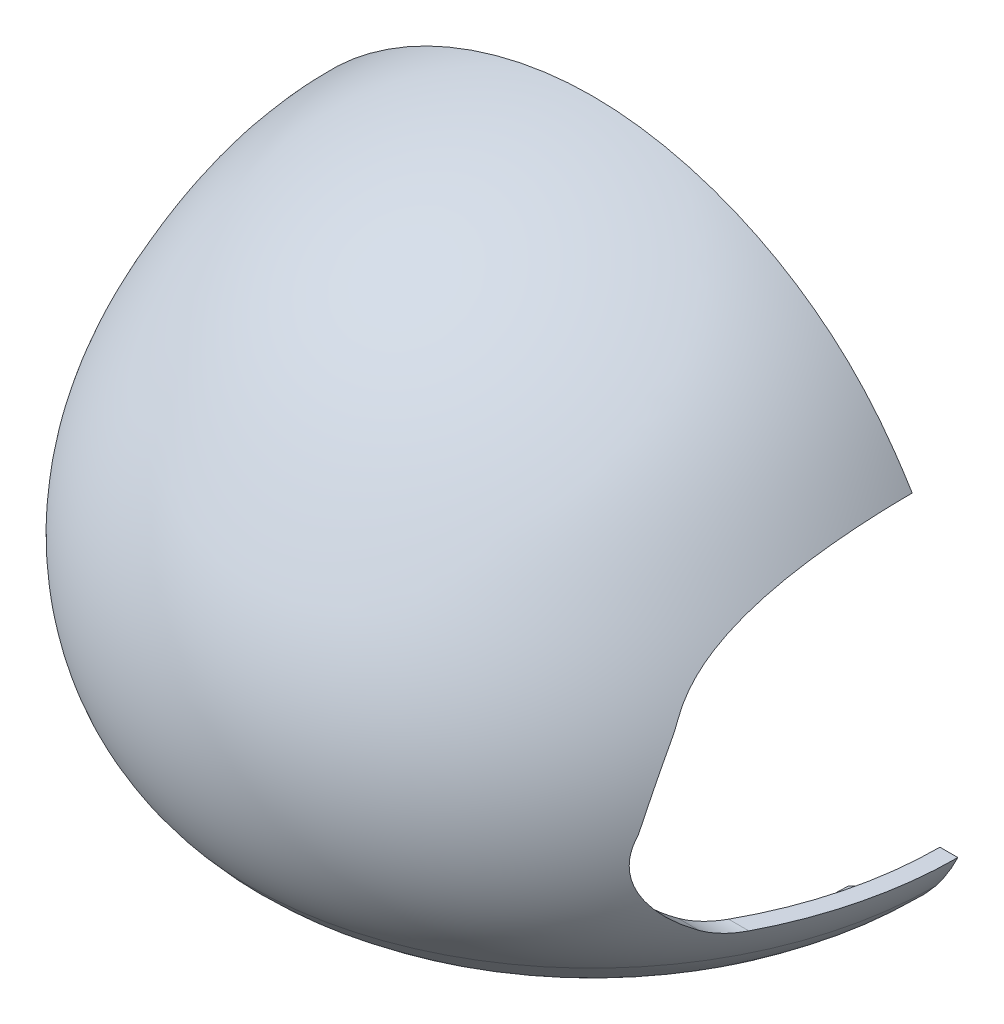
SolidWorks part; units mm, degrees
ref_plane "Front Plane" through (0, 0, 0) normal (0, 0, 1) x (1, 0, 0)
ref_plane "Top Plane" through (0, 0, 0) normal (0, 1, 0) x (1, 0, 0)
ref_plane "Right Plane" through (0, 0, 0) normal (1, 0, 0) x (0, 0, -1)
sketch "Sketch3" plane through (0, 0, 0) normal (0, 0, 1) x (1, 0, 0)
  line L0 (0.0245, 157.0849) -> (0.0245, 152.0849)
  line L1 (0.0245, -20.9434) -> (0.0245, -25.9434)
  line L2 (0.0245, 171.6103) -> (0.0245, -40.6784) construction
  spline S0 degree 3 poles (-103.1746, 0) (-78.8328, -30.0641) (-33.4587, -20.9434) (0.0245, -20.9434) knots 0 0 0 0 1 1 1 1
  spline S1 degree 3 poles (-103.1746, 0) (-114.7602, 14.5762) (-119.8367, 49.2728) (-101.4518, 88.6739) (-71.3798, 134.4794) (-29.75, 152.0849) (0.0245, 152.0849) knots 0 0 0 0 0.250738 0.442513 0.587645 1 1 1 1
  spline S2 degree 1 poles (-107.0747, -3.1288) (0.0245, -25.9434) knots 0 0 1 1 construction
  spline S3 degree 1 poles (-107.0747, -3.1288) (0.0245, 157.0849) knots 0 0 1 1 construction
  spline S4 degree 3 poles (0.0245, -25.9434) (-1.0078, -25.9434) (-3.0527, -25.9607) (-7.3007, -26.054) (-12.7748, -26.2598) (-19.5869, -26.581) (-28.9113, -27.0143) (-40.9004, -27.387) (-55.4438, -26.9753) (-69.7899, -25.0863) (-81.2787, -21.7225) (-89.9598, -17.6028) (-96.1383, -13.7178) (-100.9459, -9.7522) (-104.5344, -6.1303) (-106.2545, -4.1419) (-107.0747, -3.1288) knots -0.000194 -0.000194 -0.000194 -0.000194 0.031062 0.062318 0.12483 0.187342 0.249854 0.374879 0.499903 0.624927 0.749951 0.812464 0.874976 0.937488 0.968744 1 1 1 1
  spline S5 degree 3 poles (-107.0747, -3.1288) (-107.8617, -2.1388) (-109.3756, -0.1005) (-112.0955, 4.1156) (-114.956, 9.6441) (-117.5537, 16.5853) (-119.9627, 26.1346) (-121.1031, 38.4065) (-119.7936, 53.0884) (-116.0899, 67.0475) (-110.6339, 80.233) (-104.0343, 92.719) (-96.8153, 104.7516) (-88.5122, 116.2468) (-78.6677, 126.6978) (-67.4647, 135.7136) (-55.1826, 143.2806) (-42.0542, 149.311) (-28.3211, 153.7314) (-14.2042, 156.4574) (-4.7225, 157.0849) (0.0245, 157.0849) knots -0.000101 -0.000101 -0.000101 -0.000101 0.015525 0.031152 0.062405 0.093658 0.124911 0.187418 0.249924 0.31243 0.374937 0.437443 0.499949 0.562456 0.624962 0.687468 0.749975 0.812481 0.874987 0.937494 1 1 1 1
  dimension "D1" = 5
revolve "Revolve5" add sketch "Sketch3" angle 360 about L2
ref_plane "Plane2" through (0, -30, 0) normal (0, 1, 0) x (1, 0, 0)
sketch "Sketch4" plane through (0, -30, 0) normal (0, 1, 0) x (1, 0, 0)
  circle A0 centre (0, 0) radius 80.1001
extrude "Cut-Extrude2" cut sketch "Sketch4" along normal blind 20
sketch "Sketch5" plane through (0, 0, 0) normal (1, 0, 0) x (0, 0, -1)
  line L0 (-52.4765, 8.1366) -> (52.4765, 8.1366)
  arc A0 (-52.4765, 8.1366) -> (-63.3365, 11.3419) centre (-52.4765, 28.1366) cw
  arc A1 (52.4765, 8.1366) -> (63.3365, 11.3419) centre (52.4765, 28.1366) ccw
  arc A2 (-69.3418, 64.1464) -> (-67.0221, 68.7237) centre (-184.1186, 125.1898) ccw
  arc A3 (70.4941, 63.0471) -> (66.203, 70.3101) centre (188.8284, 137.8602) cw
  arc A4 (78.7462, 39.318) -> (77.2009, 46.2401) centre (214.5664, 73.272) cw
  ellipse E0 centre (0, 56.3684) end of major axis (69.9377, 56.3684) minor radius 43.2422 (66.203, 70.3101) -> (-67.0221, 68.7237) ccw
  ellipse E1 centre (0, 34.6362) end of major axis (79.3292, 34.6362) minor radius 38.6866 (-77.8366, 42.1057) -> (-63.3365, 11.3419) ccw
  ellipse E2 centre (0, 34.6362) end of major axis (79.3292, 34.6362) minor radius 38.6866 (63.3365, 11.3419) -> (78.7462, 39.318) ccw
  spline S0 degree 3 poles (-69.3418, 64.1464) (-73.0617, 57.1522) (-75.8989, 49.7908) (-77.8366, 42.1057) knots 0.114274 0.114274 0.114274 0.114274 1 1 1 1
  spline S1 degree 3 poles (70.4941, 63.0471) (72.3563, 60.1016) (75.0451, 54.6733) (76.6927, 48.8224) (77.2009, 46.2401) knots 0.168182 0.168182 0.168182 0.168182 0.552819 0.845618 0.845618 0.845618 0.845618
  dimension "D1" = 20
  dimension "D2" = 130
  dimension "D3" = 140
  dimension "D4" = 140
extrude "Cut-Extrude3" cut sketch "Sketch5" along normal through all
scale "Scale2" bodies to scale 106 scale about centroid uniform scaling yes scale factor 1
ref_plane "Plane3" through (0, 105, 0) normal (0, 1, 0) x (1, 0, 0)
sketch "Sketch6" plane through (0, 105, 0) normal (0, 1, 0) x (1, 0, 0)
  circle A0 centre (0, 0) radius 10
extrude "Boss-Extrude1" add sketch "Sketch6" against normal up to surface (46.603 mm away)
sketch "Sketch7" plane through (0, 0, 0) normal (0, 0, 1) x (1, 0, 0)
  line L1 (174.4564, -182.2964) -> (-174.4564, -182.2964)
  line L2 (174.4564, -182.2964) -> (174.4564, 182.2964)
  line L3 (174.4564, 182.2964) -> (-174.4564, 182.2964)
  line L4 (-174.4564, -182.2964) -> (-174.4564, 182.2964)
  line L5 (174.4564, -182.2964) -> (-174.4564, 182.2964) construction
  line L6 (174.4564, 182.2964) -> (-174.4564, -182.2964) construction
  point P0 (0, 0)
extrude "Cut-Extrude4" cut sketch "Sketch7" against normal blind 159
